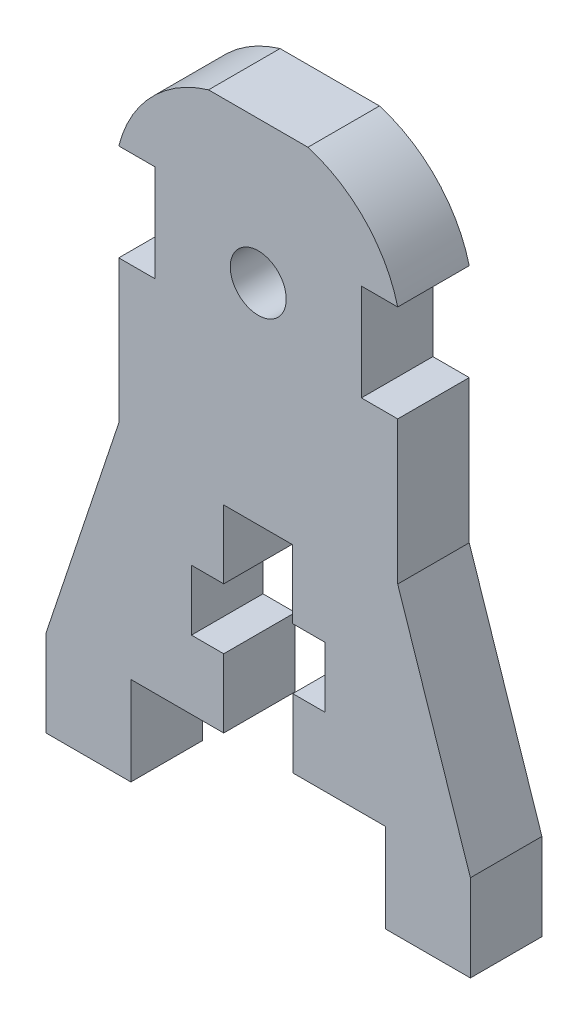
SolidWorks part; units mm, degrees
ref_plane "Front Plane" through (0, 0, 0) normal (0, 0, 1) x (1, 0, 0)
ref_plane "Top Plane" through (0, 0, 0) normal (0, 1, 0) x (1, 0, 0)
ref_plane "Right Plane" through (0, 0, 0) normal (1, 0, 0) x (0, 0, -1)
sketch "Sketch1" plane through (0, 0, 0) normal (0, 0, 1) x (1, 0, 0)
  line L28 (-46.2053, 0) -> (-46.2053, 6.069)
  line L82 (-46.2053, 6.069) -> (-41.1253, 21.309)
  line L83 (-41.1253, 21.309) -> (-41.1253, 31.309)
  line L84 (-41.1253, 31.309) -> (-38.5853, 31.309)
  line L85 (-38.5853, 31.309) -> (-38.5853, 38.082)
  line L86 (-38.5853, 38.082) -> (-41.1253, 38.082)
  line L87 (-46.2053, 0) -> (-40.2783, 0)
  line L88 (-40.2783, 0) -> (-40.2783, 6.209)
  line L89 (-40.2783, 6.209) -> (-33.7883, 6.209)
  line L90 (-33.7883, 6.209) -> (-33.7883, 11.008)
  line L91 (-33.7883, 11.008) -> (-36.0453, 11.008)
  line L92 (-36.0453, 11.008) -> (-36.0453, 15.241)
  line L93 (-36.0453, 15.241) -> (-33.7873, 15.241)
  line L94 (-33.7873, 15.241) -> (-33.7873, 20.019)
  line L95 (-33.7873, 20.019) -> (-28.9633, 20.019)
  line L96 (-31.3753, 20.019) -> (-31.3753, 15.222)
  line L110 (-34.8506, 44.6171) -> (-31.3662, 44.6171)
  line L111 (-31.3753, 34.659) -> (-31.3753, -6.6875) construction
  line L112 (0, 0) -> (-40.2783, 0) construction
  line L113 (-16.5453, 0) -> (-22.4723, 0)
  line L114 (-27.9001, 44.6171) -> (-31.3845, 44.6171)
  line L115 (-28.9633, 15.241) -> (-28.9633, 20.019)
  line L116 (-26.7053, 15.241) -> (-28.9633, 15.241)
  line L117 (-26.7053, 11.008) -> (-26.7053, 15.241)
  line L118 (-28.9623, 11.008) -> (-26.7053, 11.008)
  line L119 (-28.9623, 6.209) -> (-28.9623, 11.008)
  line L120 (-22.4723, 6.209) -> (-28.9623, 6.209)
  line L121 (-22.4723, 0) -> (-22.4723, 6.209)
  line L122 (-24.1653, 38.082) -> (-21.6253, 38.082)
  line L123 (-24.1653, 31.309) -> (-24.1653, 38.082)
  line L124 (-21.6253, 31.309) -> (-24.1653, 31.309)
  line L125 (-21.6253, 21.309) -> (-21.6253, 31.309)
  line L126 (-16.5453, 6.069) -> (-21.6253, 21.309)
  line L127 (-16.5453, 0) -> (-16.5453, 6.069)
  circle A17 centre (-31.3753, 34.659) radius 1.955
  arc A19 (-34.8506, 44.6171) -> (-41.1253, 38.082) centre (-32.2253, 35.8165) ccw
  arc A20 (-27.9001, 44.6171) -> (-21.6253, 38.082) centre (-30.5254, 35.8165) cw
  dimension "D3" = 6.49
  dimension "D15" = 3.91
  dimension "D16" = 14.64
  dimension "D4" = 5.927
  dimension "D5" = 2.54
  dimension "D6" = 7.338
  dimension "D7" = 6.773
  dimension "D8" = 10
  dimension "D9" = 15.24
  dimension "D10" = 6.069
  dimension "D11" = 40.2783
  dimension "D12" = 5.08
  dimension "D13" = 34.659
  dimension "D14" = 9.9582
  dimension "D17" = 9.75
extrude "Boss-Extrude1" add sketch "Sketch1" along normal blind 5 contours A20 L114 L110 A19 L86 L85 L84 L83 L82 L28 L87 L88 L89 L90 L91 L92 L93 L94 L95 L115 L116 L117 L118 L119 L120 L121 L113 L127 L126 L125 L124 L123 L122 A17
